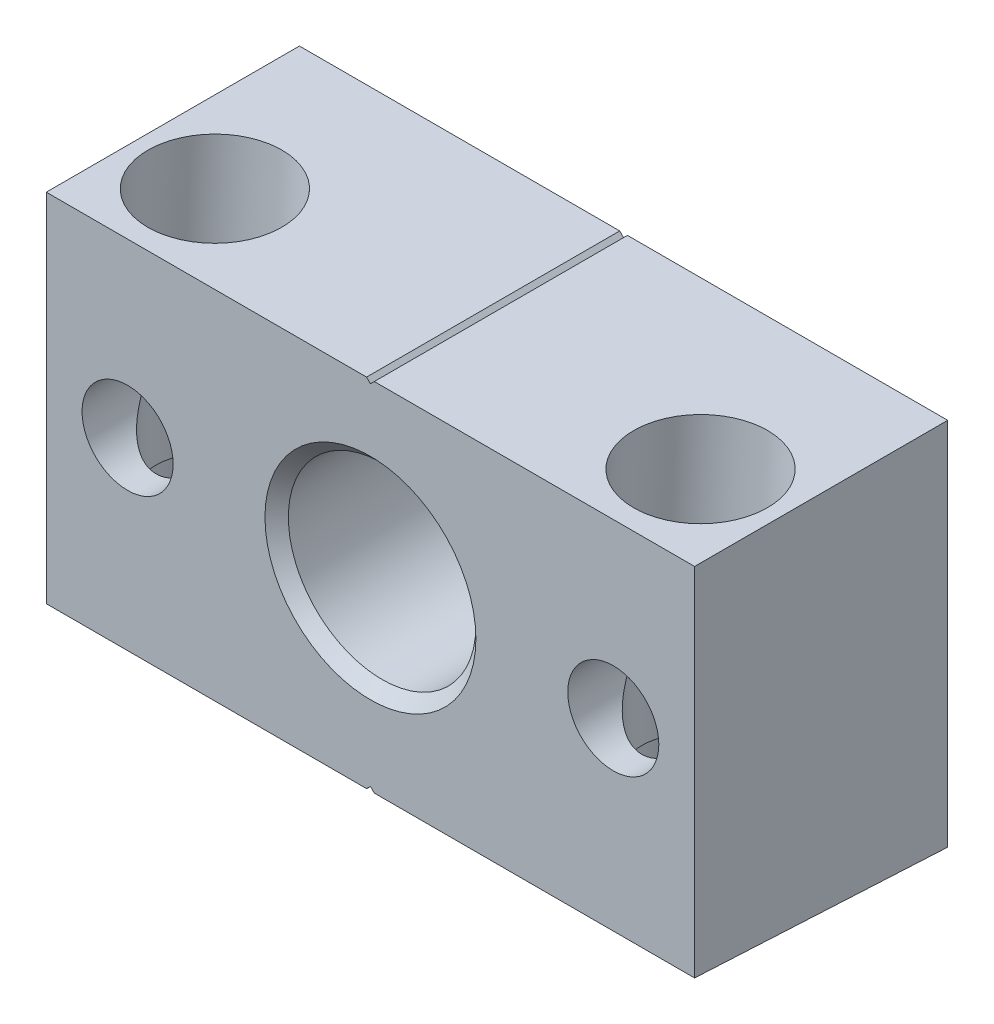
SolidWorks part; units mm, degrees
material "Alloy Steel"
ref_plane "Front Plane" through (0, 0, 0) normal (0, 0, 1) x (1, 0, 0)
ref_plane "Top Plane" through (0, 0, 0) normal (0, 1, 0) x (1, 0, 0)
ref_plane "Right Plane" through (0, 0, 0) normal (1, 0, 0) x (0, 0, -1)
sketch "Sketch1" plane through (0, 0, 0) normal (0, 0, 1) x (1, 0, 0)
  line L0 (0, 0) -> (0, 28.5118) construction
  line L1 (-32.004, 16.9926) -> (32.004, 16.9926)
  line L2 (-32.004, 16.9926) -> (-32.004, -19.5072)
  line L3 (-32.004, -19.5072) -> (32.004, -19.5072)
  line L4 (32.004, 16.9926) -> (32.004, -19.5072)
  circle A0 centre (0, 0) radius 9.2585
  circle A1 centre (-23.9776, 0) radius 4.4958
  circle A2 centre (23.9776, 0) radius 4.4958
  dimension "D4" = 18.517
  dimension "D5" = 8.9916
  dimension "D1" = 64.008
  dimension "D2" = 36.4998
  dimension "D3" = 16.9926
  dimension "D6" = 23.9776
  dimension "D7" = 47.9552
extrude "Extrude1" add sketch "Sketch1" along normal blind 24.9936
sketch "Sketch2" plane through (32.004, 0, 0) normal (1, 0, 0) x (0, 0, -1)
  line L0 (0, -19.5072) -> (-24.9936, -18.1973)
  line L1 (-24.9936, -19.5072) -> (-24.9936, 16.9926) construction
  line L2 (-24.9936, -18.1973) -> (-24.9936, -19.5072)
  line L3 (-24.9936, -19.5072) -> (0, -19.5072)
  dimension "D1" = 3
extrude "Cut-Extrude1" cut sketch "Sketch2" against normal through all
ref_plane "Plane1" through (-23.9776, 0, 0) normal (1, 0, 0) x (0, 0, -1)
sketch "Sketch3" plane through (-23.9776, 0, 0) normal (1, 0, 0) x (0, 0, -1)
  line L0 (-17.5006, 16.9318) -> (-17.5006, -17.6805) construction
  line L1 (-10.8966, -18.9361) -> (-10.8966, -8.4074)
  line L2 (0, -19.5072) -> (-24.9936, -18.1973) construction
  line L3 (-10.8966, -8.4074) -> (-12.827, -8.4074)
  line L4 (-12.827, -8.4074) -> (-12.827, 16.9926)
  line L5 (0, -19.5072) -> (0, 16.9926) construction
  line L6 (-24.9936, 16.9926) -> (0, 16.9926) construction
  line L7 (-12.827, 16.9926) -> (-17.5006, 16.9926)
  line L8 (-17.5006, 16.9926) -> (-17.5006, -18.9361)
  line L9 (-17.5006, -18.9361) -> (-10.8966, -18.9361)
  dimension "D1" = 17.5006
  dimension "D2" = 9.3472
  dimension "D3" = 13.208
  dimension "D4" = 25.4
revolve "Cut-Revolve1" cut sketch "Sketch3" angle 360 about L0
sketch "Sketch4" plane through (-23.9776, 0, 0) normal (1, 0, 0) x (0, 0, -1)
  line L0 (-16.1431, 21.4131) -> (-17.2117, 1.0225) construction
  line L1 (0, -19.5072) -> (-24.9936, -18.1973) construction
  line L2 (-9.7617, 16.9926) -> (-10.3133, 6.4682)
  line L3 (-24.9936, 16.9926) -> (0, 16.9926) construction
  line L4 (-10.3133, 6.4682) -> (-16.9082, 6.8138)
  line L5 (-16.9082, 6.8138) -> (-16.3567, 17.3382)
  line L6 (-16.3567, 17.3382) -> (-9.7617, 16.9926)
  dimension "D1" = 18.2626
  dimension "D2" = 25.4
  dimension "D3" = 13.208
revolve "Cut-Revolve2" cut sketch "Sketch4" angle 360 about L0
pattern_linear "LPattern1" count 2 spacing 47.9552 along (1, 0, 0) of "Cut-Revolve1", "Cut-Revolve2"
chamfer "Chamfer1" distance 1.1555 angle 45 2 edges at (9.2585, 0, 0) (9.2585, 0, 24.9936)
sketch "Sketch5" plane through (0, 0, 0) normal (0, 0, -1) x (-1, 0, 0)
  line L0 (-0.381, 16.9926) -> (0, 16.6116)
  line L1 (-32.004, 16.9926) -> (32.004, 16.9926) construction
  line L2 (0, 16.6116) -> (0.381, 16.9926)
  line L3 (0.381, 16.9926) -> (-0.381, 16.9926)
  line L4 (0, 0) -> (0, 23.7254) construction
  dimension "D1" = 90
  dimension "D2" = 0.381
extrude "Cut-Extrude2" cut sketch "Sketch5" against normal through all
ref_plane "Plane2" through (0, -0.0534, -1.0195) normal (0, -0.0523, -0.9986) x (-1, 0, 0)
sketch "Sketch6" plane through (0, -0.0534, -1.0195) normal (0, -0.0523, -0.9986) x (-1, 0, 0)
  line L0 (0.381, -19.4805) -> (0, -19.0995)
  line L1 (32.004, -19.4805) -> (-32.004, -19.4805) construction
  line L2 (0, -19.0995) -> (-0.381, -19.4805)
  line L3 (0, 0) -> (0, -29.5062) construction
  line L4 (0.381, -19.4805) -> (-0.381, -19.4805)
  dimension "D1" = 0.381
extrude "Cut-Extrude3" cut sketch "Sketch6" against normal through all
